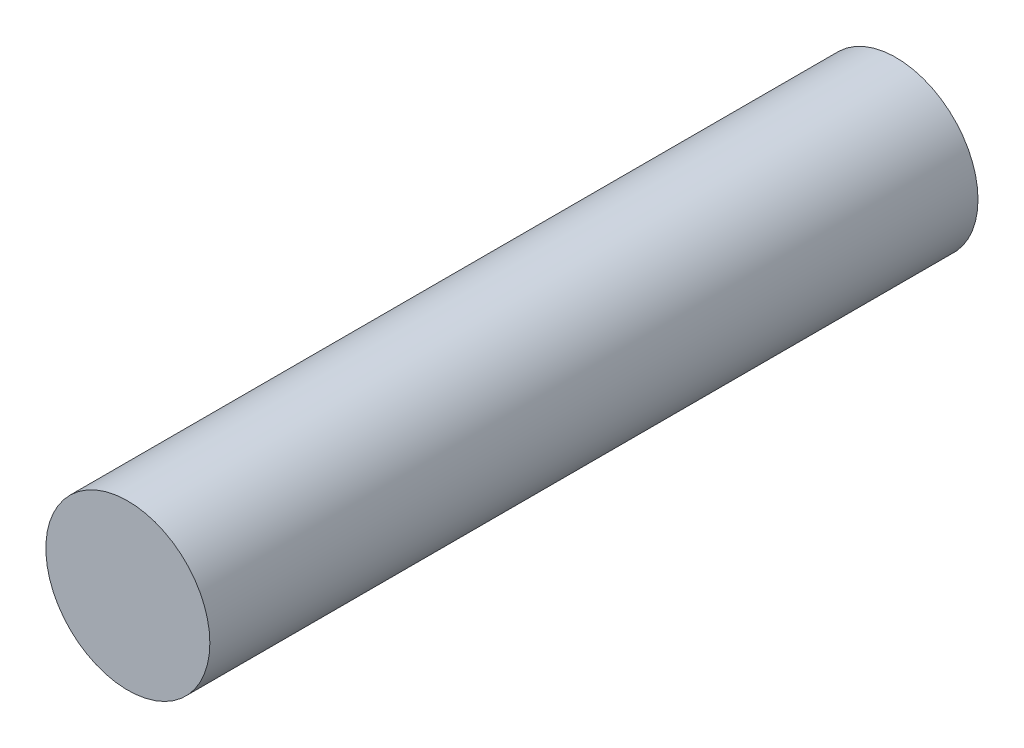
SolidWorks part; units mm, degrees
material "Custom Plastic"
ref_plane "Front Plane" through (0, 0, 0) normal (0, 0, 1) x (1, 0, 0)
ref_plane "Top Plane" through (0, 0, 0) normal (0, 1, 0) x (1, 0, 0)
ref_plane "Right Plane" through (0, 0, 0) normal (1, 0, 0) x (0, 0, -1)
sketch "Sketch1" plane through (0, 0, 0) normal (0, 0, 1) x (1, 0, 0)
  circle A0 centre (0, 0) radius 3
  dimension "D1" = 6
extrude "Boss-Extrude1" add sketch "Sketch1" along normal blind 28.1
